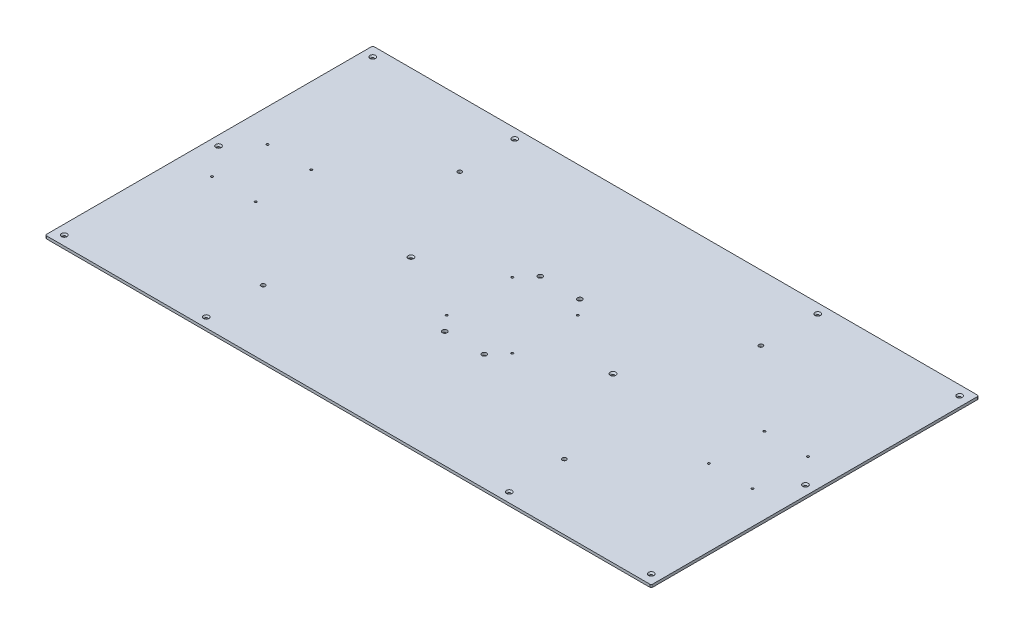
SolidWorks part; units mm, degrees
material "PC High Viscosity"
ref_plane "Front Plane" through (0, 0, 0) normal (0, 0, 1) x (1, 0, 0)
ref_plane "Top Plane" through (0, 0, 0) normal (0, 1, 0) x (1, 0, 0)
ref_plane "Right Plane" through (0, 0, 0) normal (1, 0, 0) x (0, 0, -1)
sketch "Sketch1" plane through (0, 0, 0) normal (0, 1, 0) x (1, 0, 0)
  line L1 (0, 0) -> (1409.7, 0)
  line L2 (0, 0) -> (0, 762)
  line L3 (0, 762) -> (1409.7, 762)
  line L4 (1409.7, 0) -> (1409.7, 762)
  dimension "D1" = 1409.7
  dimension "D2" = 762
extrude "Boss-Extrude1" add sketch "Sketch1" along normal blind 6.35
hole_wizard "CSK for 1/4 Flat Head Machine Screw (100)1" positions "Sketch2" profile "Sketch3" countersink size "1/4" standard "ANSI Inch"
sketch "Sketch2" plane through (0, 6.35, 0) normal (0, 1, 0) x (1, 0, 0)
  line L0 (0, 0) -> (1320.8, 0) construction
  line L1 (0, 762) -> (0, 0) construction
  line L2 (1320.8, 0) -> (1320.8, 762) construction
  line L3 (1320.8, 762) -> (0, 762) construction
  point P0 (50.8, 31.75)
  point P2 (457.2, 31.75)
  point P4 (863.6, 31.75)
  point P6 (1270, 31.75)
  point P8 (1298.575, 95.25)
  point P10 (1298.575, 666.75)
  point P12 (1270, 730.25)
  point P14 (863.6, 730.25)
  point P16 (457.2, 730.25)
  point P18 (50.8, 730.25)
  point P20 (22.225, 666.75)
  point P22 (22.225, 95.25)
  dimension "D1" = 31.75
  dimension "D2" = 22.225
  dimension "D3" = 22.225
  dimension "D4" = 95.25
  dimension "D5" = 95.25
  dimension "D6" = 31.75
  dimension "D7" = 50.8
  dimension "D8" = 50.8
  dimension "D9" = 406.4
  dimension "D10" = 406.4
sketch "Sketch3" plane through (50.8, 6.35, -31.75) normal (1, 0, 0) x (0, 0, 1)
  line L0 (0, 0) -> (0, 6.35)
  line L1 (0, 6.35) -> (3.3782, 6.35)
  line L2 (3.3782, 6.35) -> (3.3782, 2.5682)
  line L3 (3.3782, 2.5682) -> (6.4389, 0)
  line L5 (6.4389, 0) -> (0, 0)
  line L6 (-3.3782, 2.5682) -> (-6.4389, 0) construction
  line L11 (0, -6.35) -> (0, 107.95) construction
  dimension "Thru Hole Dia." = 6.7564
  dimension "Thru Hole Depth" = 6.35
  dimension "Near C'Sink Dia." = 12.8778
  dimension "Near C'Sink Angle" = 100
hole_wizard "CSK for 1/4 Flat Head Machine Screw1" positions "Sketch4" profile "Sketch5" countersink size "1/4" standard "ANSI Inch" end condition through all
sketch "Sketch4" plane through (0, 6.35, 0) normal (0, 1, 0) x (1, 0, 0)
  line L0 (0, 381) -> (224.619, 381) construction
  line L1 (0, 762) -> (0, 0) construction
  line L3 (1409.7, 0) -> (1409.7, 762) construction
  line L4 (0, 0) -> (1409.7, 0) construction
  line L5 (1409.7, 762) -> (0, 762) construction
  line L6 (704.85, 762) -> (704.85, -19.964) construction
  point P8 (1387.475, 739.775)
  point P10 (1057.275, 739.775)
  point P12 (352.425, 739.775)
  point P14 (22.225, 739.775)
  point P37 (1387.475, 22.225)
  point P39 (939.8, 381)
  point P41 (1057.275, 22.225)
  point P43 (469.9, 381)
  point P45 (352.425, 22.225)
  point P47 (22.225, 22.225)
  point P76 (1387.475, 381)
  point P78 (22.225, 381)
  dimension "D3" = 469.9
  dimension "D6" = 22.225
  dimension "D7" = 22.225
  dimension "D8" = 22.225
  dimension "D9" = 22.225
  dimension "D11" = 704.85
  dimension "D10" = 352.425
  dimension "D4" = 352.425
  dimension "D5" = 352.425
sketch "Sketch5" plane through (1387.475, 6.35, -739.775) normal (1, 0, 0) x (0, 0, 1)
  line L0 (0, 0) -> (0, 6.35)
  line L1 (0, 6.35) -> (3.3782, 6.35)
  line L2 (3.3782, 6.35) -> (3.3782, 3.5209)
  line L3 (3.3782, 3.5209) -> (6.4389, 0)
  line L5 (6.4389, 0) -> (0, 0)
  line L6 (-3.3782, 3.5209) -> (-6.4389, 0) construction
  line L11 (0, -6.35) -> (0, 107.95) construction
  dimension "Thru Hole Dia." = 6.7564
  dimension "Thru Hole Depth" = 6.35
  dimension "Near C'Sink Dia." = 12.8778
  dimension "Near C'Sink Angle" = 82
hole_wizard "#8 (0.199) Diameter Hole2" positions "Sketch7" profile "Sketch8" hole size "#8" standard "ANSI Inch" end condition through all
sketch "Sketch7" plane through (0, 0, 0) normal (0, -1, 0) x (-1, 0, 0)
  line L0 (-781.1822, 305.3079) -> (-628.5178, 457.9723) construction
  line L2 (-781.1822, 457.9723) -> (-628.5178, 305.3079) construction
  line L4 (-1409.7, 381) -> (0, 381) construction
  line L5 (-1409.7, 0) -> (-1409.7, 762) construction
  line L6 (0, 762) -> (0, 0) construction
  line L8 (-704.85, 762) -> (-704.85, 0) construction
  line L9 (-1409.7, 762) -> (0, 762) construction
  line L10 (0, 0) -> (-1409.7, 0) construction
  line L12 (-704.85, 489.5901) -> (-704.85, 273.6901) construction
  circle A0 centre (-704.85, 381.6401) radius 107.95 construction
  point P0 (-628.5178, 305.3079)
  point P2 (-628.5178, 457.9723)
  point P4 (-781.1822, 305.3079)
  point P6 (-781.1822, 457.9723)
  dimension "D1" = 152.6644
  dimension "D2" = 152.6644
  dimension "D3" = 152.6644
  dimension "D4" = 152.6644
sketch "Sketch8" plane through (628.5178, 0, -305.3079) normal (1, 0, 0) x (0, 0, -1)
  line L0 (0, 0) -> (0, 6.35)
  line L1 (0, 6.35) -> (2.5273, 6.35)
  line L2 (2.5273, 6.35) -> (2.5273, 0)
  line L5 (2.5273, 0) -> (0, 0)
  line L11 (0, -6.35) -> (0, 107.95) construction
  dimension "Thru Hole Dia." = 5.0546
  dimension "Thru Hole Depth" = 6.35
hole_wizard "7/16 (0.4375) Diameter Hole1" positions "Sketch9" profile "Sketch10" hole size "7/16" standard "ANSI Inch" end condition through all
sketch "Sketch9" plane through (0, 6.35, 0) normal (0, 1, 0) x (1, 0, 0)
  line L0 (750.8701, 270.5377) -> (658.8299, 492.7424) construction
  line L2 (704.85, 762) -> (704.85, 1.2802) construction
  line L3 (1409.7, 762) -> (0, 762) construction
  line L5 (1409.7, 381) -> (-36.3244, 381) construction
  line L6 (1409.7, 0) -> (1409.7, 762) construction
  line L7 (658.8299, 270.5377) -> (704.85, 381.6401) construction
  line L9 (704.85, 381.6401) -> (750.8701, 492.7424) construction
  circle A0 centre (704.85, 381.6401) radius 120.2563 construction
  point P0 (658.8299, 492.7424)
  point P2 (750.8701, 270.5377)
  point P27 (658.8299, 270.5377)
  point P29 (750.8701, 492.7424)
  dimension "D1" = 240.5126
  dimension "D2" = 22.5
  dimension "D3" = 22.5
  dimension "D4" = 22.5
sketch "Sketch10" plane through (658.8299, 6.35, -492.7424) normal (1, 0, 0) x (0, 0, 1)
  line L0 (0, 0) -> (0, 6.35)
  line L1 (0, 6.35) -> (5.5562, 6.35)
  line L2 (5.5562, 6.35) -> (5.5562, 0)
  line L5 (5.5562, 0) -> (0, 0)
  line L11 (0, -6.35) -> (0, 107.95) construction
  dimension "Thru Hole Dia." = 11.1125
  dimension "Thru Hole Depth" = 6.35
hole_wizard "#8 (0.199) Diameter Hole1" positions "Sketch11" profile "Sketch12" hole size "#8" standard "ANSI Inch" end condition through all
sketch "Sketch11" plane through (0, 6.35, 0) normal (0, 1, 0) x (1, 0, 0)
  line L0 (1409.7, 0) -> (1409.7, 762) construction
  line L1 (0, 0) -> (1409.7, 0) construction
  line L2 (704.85, 0) -> (704.85, 762) construction
  line L3 (1409.7, 762) -> (0, 762) construction
  line L6 (0, 762) -> (0, 0) construction
  line L7 (0, 0) -> (1409.7, 0) construction
  point P0 (1333.5, 311.6847)
  point P2 (1231.9, 311.6847)
  point P4 (1231.9, 441.0659)
  point P6 (1333.5, 441.0659)
  point P26 (76.2, 441.0659)
  point P27 (177.8, 441.0659)
  point P28 (177.8, 311.6847)
  point P29 (76.2, 311.6847)
  dimension "D1" = 76.2
  dimension "D2" = 129.3812
  dimension "D3" = 101.6
  dimension "D4" = 101.6
  dimension "D5" = 129.3813
  dimension "D6" = 76.2
  dimension "D7" = 441.0659
  dimension "D8" = 129.3812
sketch "Sketch12" plane through (1333.5, 6.35, -311.6847) normal (1, 0, 0) x (0, 0, 1)
  line L0 (0, 0) -> (0, 6.35)
  line L1 (0, 6.35) -> (2.5273, 6.35)
  line L2 (2.5273, 6.35) -> (2.5273, 0)
  line L5 (2.5273, 0) -> (0, 0)
  line L11 (0, -6.35) -> (0, 107.95) construction
  dimension "Thru Hole Dia." = 5.0546
  dimension "Thru Hole Depth" = 6.35
hole_wizard "3/8 (0.375) Diameter Hole1" positions "Sketch13" profile "Sketch14" hole size "3/8" standard "ANSI Inch" end condition through all
sketch "Sketch13" plane through (0, 6.35, 0) normal (0, 1, 0) x (1, 0, 0)
  line L0 (704.85, 0) -> (704.85, 762) construction
  line L1 (0, 0) -> (1409.7, 0) construction
  line L2 (1409.7, 762) -> (0, 762) construction
  line L4 (0, 381) -> (1332.106, 381) construction
  line L5 (0, 762) -> (0, 0) construction
  circle A0 centre (354.5328, 152.4) radius 14.2875 construction
  circle A1 centre (704.85, 381) radius 404.0188 construction
  circle A2 centre (354.5328, 609.6) radius 14.2875 construction
  circle A3 centre (1055.1672, 152.4) radius 14.2875 construction
  circle A4 centre (1055.1672, 609.6) radius 14.2875 construction
  point P0 (354.5328, 152.4)
  point P2 (354.5328, 609.6)
  point P4 (1055.1672, 609.6)
  point P6 (1055.1672, 152.4)
  dimension "D1" = 28.575
  dimension "D2" = 808.0375
  dimension "D3" = 152.4
  dimension "D4" = 354.5328
sketch "Sketch14" plane through (354.5328, 6.35, -152.4) normal (1, 0, 0) x (0, 0, 1)
  line L0 (0, 0) -> (0, 6.35)
  line L1 (0, 6.35) -> (4.7625, 6.35)
  line L2 (4.7625, 6.35) -> (4.7625, 0)
  line L5 (4.7625, 0) -> (0, 0)
  line L11 (0, -6.35) -> (0, 107.95) construction
  dimension "Thru Hole Dia." = 9.525
  dimension "Thru Hole Depth" = 6.35
fillet "Fillet1" radius 3.175 4 edges at (1409.7, 3.175, -762) (0, 3.175, -762) (0, 3.175, 0) (1409.7, 3.175, 0)
equation "\"D3@Sketch2\"=\"D2@Sketch2\""
equation "\"D5@Sketch2\"=\"D4@Sketch2\""
equation "\"D4@Sketch4\"=\"D11@Sketch4\"/2"
equation "\"D5@Sketch4\"=\"D11@Sketch4\"/2"
equation "\"D3@Sketch4\"=55.5/3"
